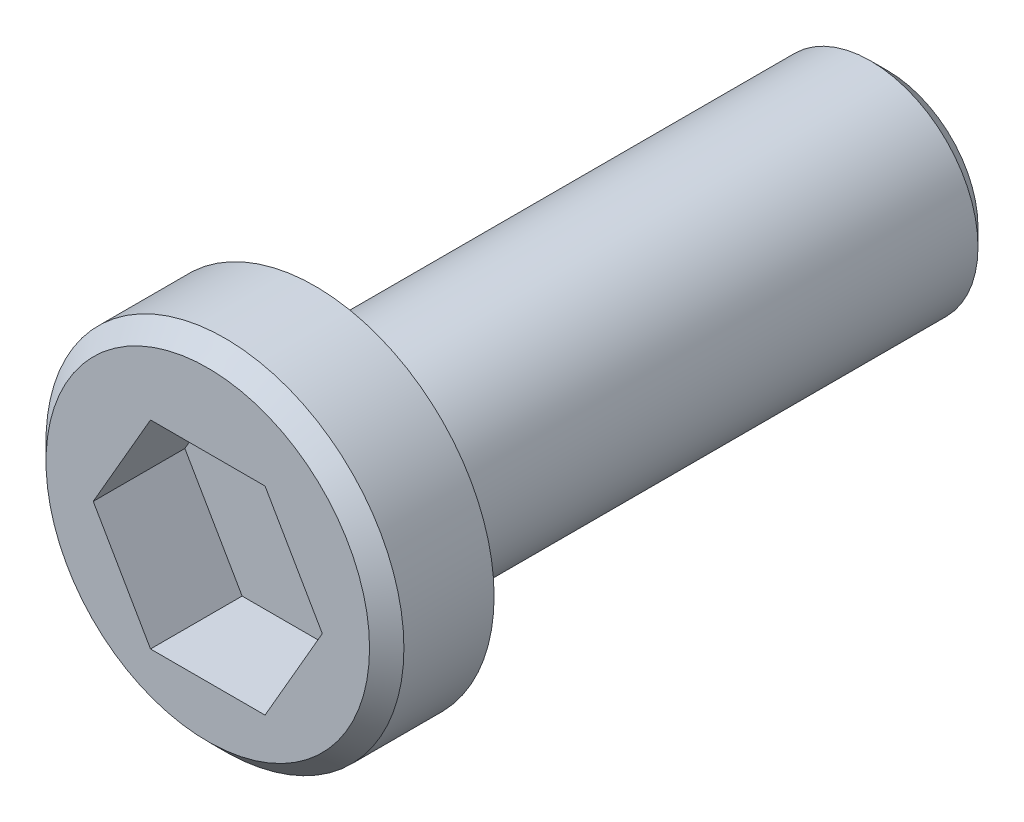
SolidWorks part; units mm, degrees
material "Plain Carbon Steel"
ref_plane "Front" through (0, 0, 0) normal (0, 0, 1) x (1, 0, 0)
ref_plane "Top" through (0, 0, 0) normal (0, 1, 0) x (1, 0, 0)
ref_plane "Right" through (0, 0, 0) normal (1, 0, 0) x (0, 0, -1)
sketch "Sketch1" plane through (0, 0, 0) normal (0, 0, 1) x (1, 0, 0)
  circle A0 centre (0, 0) radius 4.7625
  dimension "D1" = 9.525
extrude "Extrude1" add sketch "Sketch1" along normal blind 25.4
sketch "Sketch3" plane through (0, 0, 25.4) normal (0, 0, 1) x (1, 0, 0)
  circle A0 centre (0, 0.4916) radius 7.9375
  dimension "D1" = 15.875
extrude "Extrude3" add sketch "Sketch3" along normal blind 4.7625
chamfer "Chamfer1" distance 0.762 angle 45 2 edges at (4.7625, 0, 0) (7.9375, 0.4916, 30.1625)
sketch "Sketch4" plane through (0, 0, 30.1625) normal (0, 0, 1) x (1, 0, 0)
  line L0 (8.7312, 0) -> (-8.7312, 0) construction
  line L1 (5.08, 0) -> (2.54, 4.3994)
  line L2 (2.54, 4.3994) -> (-2.54, 4.3994)
  line L3 (-2.54, 4.3994) -> (-5.08, 0)
  line L4 (-5.08, 0) -> (-2.54, -4.3994)
  line L5 (-2.54, -4.3994) -> (2.54, -4.3994)
  line L6 (2.54, -4.3994) -> (5.08, 0)
  circle A0 centre (0, 0) radius 4.3994 construction
  dimension "D1" = 5.08
extrude "Cut-Extrude1" cut sketch "Sketch4" against normal blind 4.064
